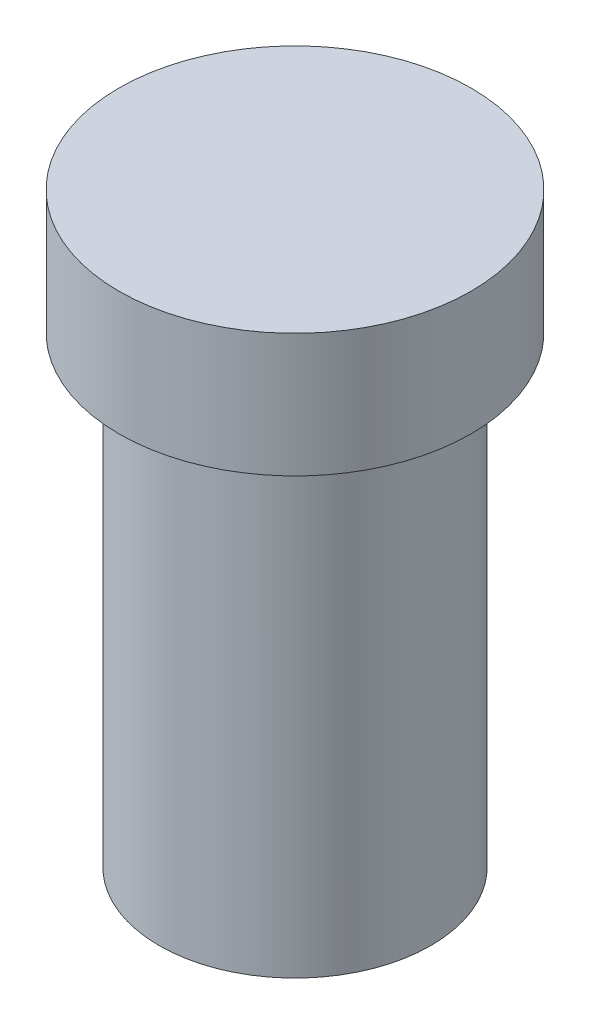
SolidWorks part; units mm, degrees
ref_plane "Front Plane" through (0, 0, 0) normal (0, 0, 1) x (1, 0, 0)
ref_plane "Top Plane" through (0, 0, 0) normal (0, 1, 0) x (1, 0, 0)
ref_plane "Right Plane" through (0, 0, 0) normal (1, 0, 0) x (0, 0, -1)
sketch "Sketch1" plane through (0, 0, 0) normal (0, 1, 0) x (1, 0, 0)
  circle A0 centre (0, 0) radius 28.5
  dimension "D1" = 57
extrude "Boss-Extrude1" add sketch "Sketch1" against normal blind 20
sketch "Sketch2" plane through (0, -20, 0) normal (0, -1, 0) x (1, 0, 0)
  circle A0 centre (0, 0) radius 22
  dimension "D1" = 44
extrude "Boss-Extrude2" add sketch "Sketch2" along normal blind 75
